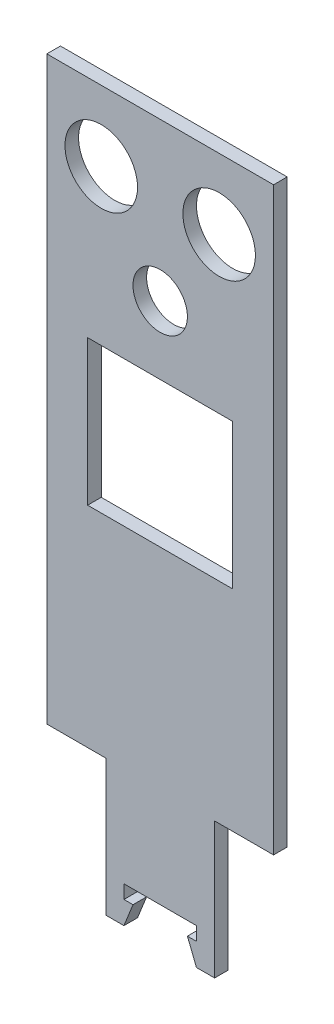
SolidWorks part; units mm, degrees
ref_plane "Alzado" through (0, 0, 0) normal (0, 0, 1) x (1, 0, 0)
ref_plane "Planta" through (0, 0, 0) normal (0, 1, 0) x (1, 0, 0)
ref_plane "Vista lateral" through (0, 0, 0) normal (1, 0, 0) x (0, 0, -1)
sketch "Model" plane through (0, 0, 0) normal (0, 0, 1) x (1, 0, 0)
  line L0 (58.7498, 90.0078) -> (58.7498, -37.9922)
  line L1 (45.7498, -37.9922) -> (58.7498, -37.9922)
  line L2 (45.7498, -67.9922) -> (45.7498, -37.9922)
  line L3 (41.7498, -67.9922) -> (45.7498, -67.9922)
  line L4 (39.7498, -62.9922) -> (41.7498, -67.9922)
  line L5 (41.7498, -62.9922) -> (39.7498, -62.9922)
  line L6 (41.7498, -59.9922) -> (41.7498, -62.9922)
  line L7 (25.7498, -59.9922) -> (41.7498, -59.9922)
  line L8 (25.7498, -62.9922) -> (25.7498, -59.9922)
  line L9 (27.7498, -62.9922) -> (25.7498, -62.9922)
  line L10 (25.7498, -67.9922) -> (27.7498, -62.9922)
  line L11 (21.7498, -67.9922) -> (25.7498, -67.9922)
  line L12 (21.7498, -37.9922) -> (21.7498, -67.9922)
  line L13 (8.7498, -37.9922) -> (21.7498, -37.9922)
  line L14 (8.7498, 90.0078) -> (8.7498, -37.9922)
  line L15 (58.7498, 90.0078) -> (8.7498, 90.0078)
  line L16 (49.7498, 40.3078) -> (49.7498, 8.3078)
  line L17 (17.7498, 40.3078) -> (49.7498, 40.3078)
  line L18 (17.7498, 8.3078) -> (17.7498, 40.3078)
  line L19 (49.7498, 8.3078) -> (17.7498, 8.3078)
  circle A0 centre (33.7498, 55.3078) radius 6
  circle A1 centre (20.7498, 74.5078) radius 8
  circle A2 centre (46.7498, 74.5078) radius 8
extrude "Saliente-Extruir1" add sketch "Model" along normal blind 3
